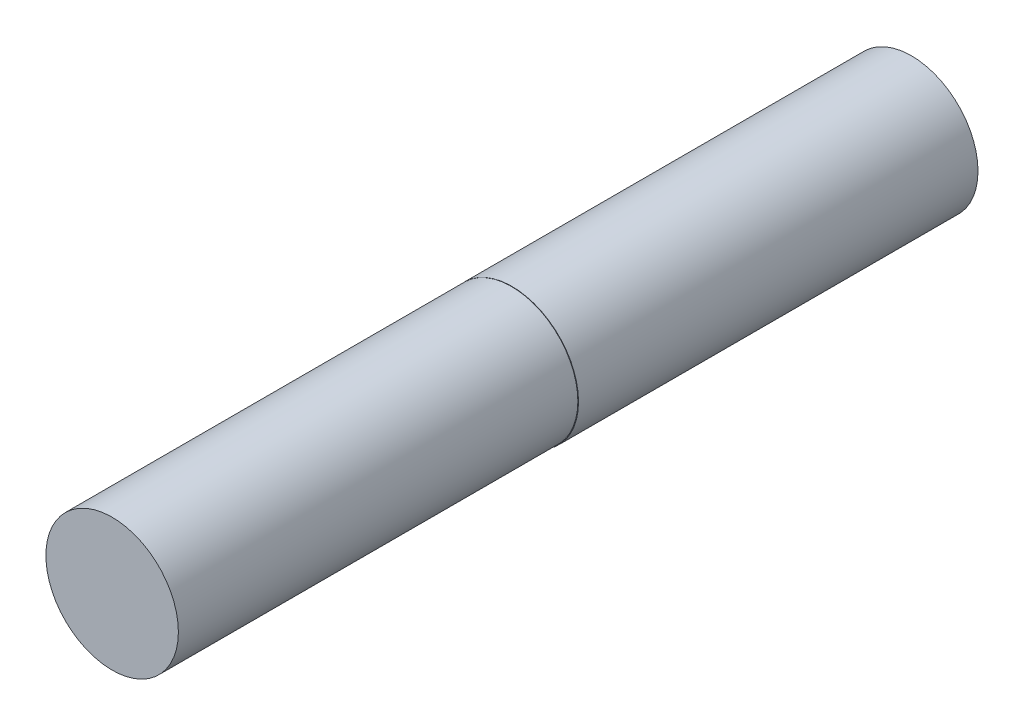
SolidWorks part; units mm, degrees
ref_plane "Front" through (0, 0, 0) normal (0, 0, 1) x (1, 0, 0)
ref_plane "Top" through (0, 0, 0) normal (0, 1, 0) x (1, 0, 0)
ref_plane "Right" through (0, 0, 0) normal (1, 0, 0) x (0, 0, -1)
sketch "Sketch1" plane through (0, 0, 0) normal (0, 0, 1) x (1, 0, 0)
  line L0 (-4.9752, 0) -> (-1.9752, 0)
  line L2 (-4.9752, 1.5) -> (-4.9752, -1.5)
  line L3 (-4.9752, -1.5) -> (-1.9752, -1.5)
  line L5 (-1.9752, 1.5) -> (-1.9752, -1.5)
  line L6 (-4.9752, 1.5) -> (-1.9752, 1.5)
  circle A0 centre (0.0248, 0) radius 5
  dimension "D1" = 10
  dimension "D2" = 1.5
  dimension "D3" = 3
extrude "Boss-Extrude1" add sketch "Sketch1" along normal blind 30 contours L3 A0 L6 L5
sketch "Sketch2" plane through (0, 0, 30) normal (0, 0, 1) x (1, 0, 0)
  circle A0 centre (0, 0) radius 4.9752
extrude "Boss-Extrude2" add sketch "Sketch2" along normal blind 30
